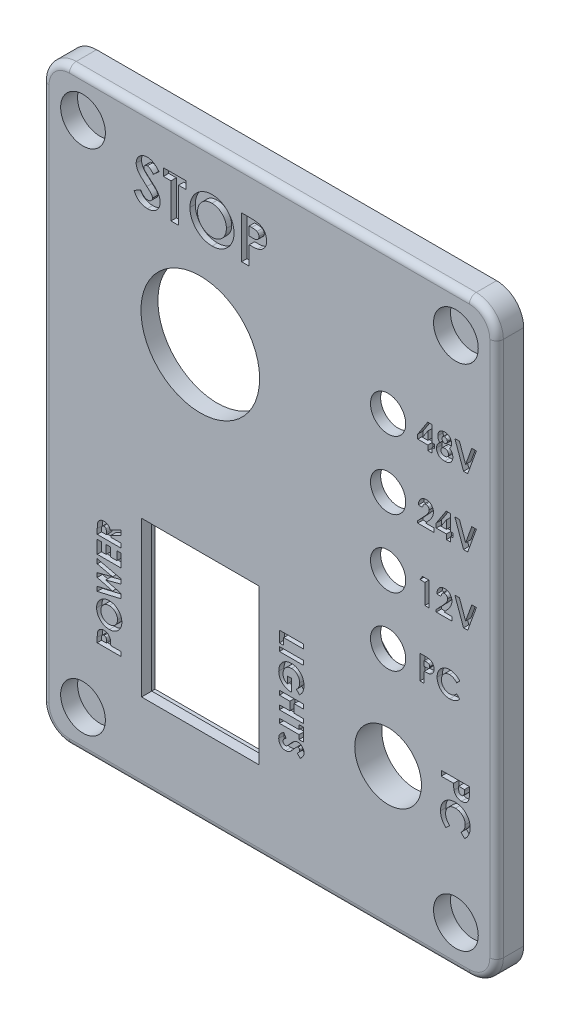
SolidWorks part; units mm, degrees
ref_plane "Front Plane" through (0, 0, 0) normal (0, 0, 1) x (1, 0, 0)
ref_plane "Top Plane" through (0, 0, 0) normal (0, 1, 0) x (1, 0, 0)
ref_plane "Right Plane" through (0, 0, 0) normal (1, 0, 0) x (0, 0, -1)
sketch "Guide Sketch" plane through (0, 0, 0) normal (0, 0, 1) x (1, 0, 0)
  line L0 (63.5, -25.4) -> (63.5, -83.2226) construction
  line L1 (0, 0) -> (82.55, 0)
  line L2 (0, 0) -> (0, -107.95)
  line L3 (0, -107.95) -> (82.55, -107.95)
  line L4 (82.55, 0) -> (82.55, -107.95)
  line L5 (15.367, -64.42) -> (41.275, -64.42)
  line L6 (15.367, -64.42) -> (15.367, -95.4588)
  line L7 (15.367, -95.4588) -> (41.275, -95.4588)
  line L8 (41.275, -64.42) -> (41.275, -95.4588)
  line L9 (15.367, -64.42) -> (41.275, -95.4588) construction
  line L10 (15.367, -95.4588) -> (41.275, -64.42) construction
  circle A0 centre (28.321, -31.75) radius 20.1549
  circle A1 centre (63.5, -25.4) radius 3.6195
  circle A2 centre (63.5, -38.1) radius 3.6195
  circle A3 centre (63.5, -50.8) radius 3.6195
  circle A4 centre (63.5, -63.5) radius 3.6195
  circle A5 centre (63.5, -82.55) radius 7.5
  circle A6 centre (6.35, -6.35) radius 2.286
  circle A7 centre (6.35, -6.35) radius 5.08
  circle A8 centre (76.2, -6.35) radius 5.08
  circle A9 centre (76.2, -6.35) radius 2.286
  circle A10 centre (76.2, -101.6) radius 5.08
  circle A11 centre (76.2, -101.6) radius 2.286
  circle A12 centre (6.35, -101.6) radius 5.08
  circle A13 centre (6.35, -101.6) radius 2.286
  point P5 (28.321, -79.9394)
  dimension "D5" = 40.3098
  dimension "D6" = 7.239
  dimension "D9" = 15
  dimension "D16" = 4.572
  dimension "D17" = 10.16
  dimension "D1" = 82.55
  dimension "D2" = 107.95
  dimension "D3" = 25.908
  dimension "D4" = 31.0388
  dimension "D8" = 19.05
  dimension "D10" = 25.4
  dimension "D11" = 15.367
  dimension "D12" = 19.05
  dimension "D13" = 12.7
  dimension "D14" = 31.75
  dimension "D15" = 28.0106
  dimension "D18" = 6.35
  dimension "D19" = 6.35
  dimension "D7" = 4
  dimension "D21" = 2
  dimension "D20" = 2
sketch "Sketch2" plane through (0, 0, 0) normal (0, 0, 1) x (1, 0, 0)
  line L6 (17.321, -65.4394) -> (39.321, -65.4394)
  line L7 (17.321, -65.4394) -> (17.321, -94.4394)
  line L8 (17.321, -94.4394) -> (39.321, -94.4394)
  line L9 (83.82, 1.27) -> (-1.27, 1.27)
  line L10 (83.82, -109.22) -> (83.82, 1.27)
  line L11 (-1.27, -109.22) -> (83.82, -109.22)
  line L12 (-1.27, 1.27) -> (-1.27, -109.22)
  line L13 (83.82, 1.27) -> (-1.27, 1.27)
  line L14 (83.82, -109.22) -> (83.82, 1.27)
  line L15 (-1.27, -109.22) -> (83.82, -109.22)
  line L16 (-1.27, 1.27) -> (-1.27, -109.22)
  line L17 (39.321, -65.4394) -> (39.321, -94.4394)
  line L18 (17.321, -65.4394) -> (39.321, -94.4394) construction
  line L19 (17.321, -94.4394) -> (39.321, -65.4394) construction
  circle A0 centre (28.321, -31.75) radius 11.1125
  circle A1 centre (63.5, -25.4) radius 3.302
  circle A2 centre (63.5, -38.1) radius 3.302
  circle A3 centre (63.5, -50.8) radius 3.302
  circle A4 centre (63.5, -63.5) radius 3.302
  circle A5 centre (63.5, -82.55) radius 6.25
  circle A6 centre (6.35, -6.35) radius 4.191
  circle A7 centre (76.2, -6.35) radius 4.191
  circle A8 centre (76.2, -101.6) radius 4.191
  circle A9 centre (6.35, -101.6) radius 4.191
  point P34 (28.321, -79.9394)
  dimension "D1" = 22.225
  dimension "D2" = 6.604
  dimension "D3" = 12.5
  dimension "D5" = 8.382
  dimension "D6" = 22
  dimension "D7" = 29
  dimension "D4" = 1.27
extrude ".125 Base" add sketch "Sketch2" along normal blind 3.175
sketch "Sketch3" plane through (0, 0, 0) normal (0, 0, -1) x (-1, 0, 0)
  line L0 (-83.82, 1.27) -> (1.27, 1.27) construction
  line L1 (-83.82, -109.22) -> (-83.82, 1.27) construction
  line L2 (1.27, -109.22) -> (-83.82, -109.22) construction
  line L3 (1.27, 1.27) -> (1.27, -109.22) construction
  line L4 (-83.82, 1.27) -> (1.27, 1.27)
  line L5 (-83.82, -109.22) -> (-83.82, 1.27)
  line L6 (1.27, -109.22) -> (-83.82, -109.22)
  line L7 (1.27, 1.27) -> (1.27, -109.22)
  line L8 (-63.5, -25.4) -> (-63.5, -63.5) construction
  line L9 (-55.88, -25.4) -> (-55.88, -63.5)
  line L10 (-71.12, -25.4) -> (-71.12, -63.5)
  line L22 (-14.781, -96.9794) -> (-14.781, -62.8994)
  line L23 (-41.861, -96.9794) -> (-14.781, -96.9794)
  line L24 (-41.861, -62.8994) -> (-41.861, -96.9794)
  line L25 (-14.781, -62.8994) -> (-41.861, -62.8994)
  line L26 (-14.781, -96.9794) -> (-14.781, -62.8994)
  line L27 (-41.861, -96.9794) -> (-14.781, -96.9794)
  line L28 (-41.861, -62.8994) -> (-41.861, -96.9794)
  line L29 (-14.781, -62.8994) -> (-41.861, -62.8994)
  circle A0 centre (-76.2, -6.35) radius 2.286 construction
  circle A1 centre (-76.2, -101.6) radius 2.286 construction
  circle A2 centre (-6.35, -101.6) radius 2.286 construction
  circle A3 centre (-6.35, -6.35) radius 2.286 construction
  circle A4 centre (-76.2, -6.35) radius 2.286
  circle A5 centre (-76.2, -101.6) radius 2.286
  circle A6 centre (-6.35, -101.6) radius 2.286
  circle A7 centre (-6.35, -6.35) radius 2.286
  arc A8 (-55.88, -25.4) -> (-71.12, -25.4) centre (-63.5, -25.4) ccw
  arc A9 (-71.12, -63.5) -> (-55.88, -63.5) centre (-63.5, -63.5) ccw
  circle A10 centre (-28.321, -31.75) radius 21.59
  circle A11 centre (-63.5, -82.55) radius 6.25 construction
  circle A12 centre (-63.5, -82.55) radius 6.25
  point P18 (-63.5, -44.45)
  dimension "D2" = 7.62
  dimension "D3" = 43.18
  dimension "D1" = 2.54
extrude ".075 Face" add sketch "Sketch3" along normal blind 1.905
sketch "Sketch4" plane through (0, 0, 0) normal (0, 0, -1) x (-1, 0, 0)
  line L0 (-55.88, -63.5) -> (-55.88, -25.4) construction
  line L1 (-71.12, -25.4) -> (-71.12, -63.5) construction
  line L2 (-41.861, -62.8994) -> (-41.861, -96.9794) construction
  line L3 (-41.861, -96.9794) -> (-14.781, -96.9794) construction
  line L4 (-14.781, -96.9794) -> (-14.781, -62.8994) construction
  line L5 (-14.781, -62.8994) -> (-41.861, -62.8994) construction
  line L6 (-55.88, -63.5) -> (-55.88, -25.4)
  line L7 (-71.12, -25.4) -> (-71.12, -63.5)
  line L8 (-41.861, -62.8994) -> (-41.861, -96.9794)
  line L9 (-41.861, -96.9794) -> (-14.781, -96.9794)
  line L10 (-14.781, -96.9794) -> (-14.781, -62.8994)
  line L11 (-14.781, -62.8994) -> (-41.861, -62.8994)
  arc A0 (-55.88, -25.4) -> (-71.12, -25.4) centre (-63.5, -25.4) ccw construction
  arc A1 (-71.12, -63.5) -> (-55.88, -63.5) centre (-63.5, -63.5) ccw construction
  arc A2 (-55.88, -25.4) -> (-71.12, -25.4) centre (-63.5, -25.4) ccw
  arc A3 (-71.12, -63.5) -> (-55.88, -63.5) centre (-63.5, -63.5) ccw
extrude "Reliefs for shallow mounts" cut sketch "Sketch4" against normal blind 1.27
fillet "Round Corners" radius 5.08 4 edges at (83.82, -109.22, 0.635) (-1.27, -109.22, 0.635) (83.82, 1.27, 0.635) (-1.27, 1.27, 0.635)
sketch "Sketch5" plane through (0, 0, 3.175) normal (0, 0, 1) x (1, 0, 0)
  line L0 (68.9384, -27.6677) -> (68.9384, -71.6036) construction
  line L1 (78.74, 1.27) -> (3.81, 1.27) construction
  line L4 (13.511, -65.4394) -> (13.511, -94.4394)
  line L5 (13.511, -65.4394) -> (13.511, -94.4394) construction
  line L6 (73.4585, -75.4005) -> (73.4585, -90.2267) construction
  line L7 (43.131, -94.4394) -> (43.131, -65.4394)
  line L8 (43.131, -94.4394) -> (43.131, -65.4394) construction
  text T0 "<b>48V</b>" font "Century Gothic" height in points 17
  text T1 "<b>24V</b>" font "Century Gothic" height in points 17
  text T2 "<b>12V</b>" font "Century Gothic" height in points 17
  text T3 "<b>PC</b>" font "Century Gothic" height in points 17
  text T4 "<b>STOP</b>" font "Century Gothic" height in points 30
  text T5 "<b>POWER</b>" font "Century Gothic" height in points 17
  text T6 "<b>LIGHTS</b>" font "Century Gothic" height in points 17
  text T7 "<b>PC</b>" font "Century Gothic" height in points 20
  dimension "D1" = 28.9377
  dimension "D2" = 12.7
  dimension "D3" = 12.7
  dimension "D4" = 12.7
  dimension "D5" = 3.81
  dimension "D6" = 3.81
extrude "Lettering" cut sketch "Sketch5" against normal blind 1
sketch "Sketch6" plane through (0, 0, 0) normal (0, 0, 1) x (1, 0, 0)
  circle A0 centre (6.35, -6.35) radius 2.286 construction
  circle A1 centre (76.2, -6.35) radius 2.286 construction
  circle A2 centre (76.2, -101.6) radius 2.286 construction
  circle A3 centre (6.35, -101.6) radius 2.286 construction
  circle A4 centre (6.35, -6.35) radius 2.286
  circle A5 centre (76.2, -6.35) radius 2.286
  circle A6 centre (76.2, -101.6) radius 2.286
  circle A7 centre (6.35, -101.6) radius 2.286
extrude "Support Material" add sketch "Sketch6" against normal blind 0.2
fillet "Fillet2" radius 1.27 8 edges at (0.2179, -0.2179, 3.175) (41.275, 1.27, 3.175) (82.3321, -0.2179, 3.175) (83.82, -53.975, 3.175) (82.3321, -107.7321, 3.175) (41.275, -109.22, 3.175) (0.2179, -107.7321, 3.175) (-1.27, -53.975, 3.175)
